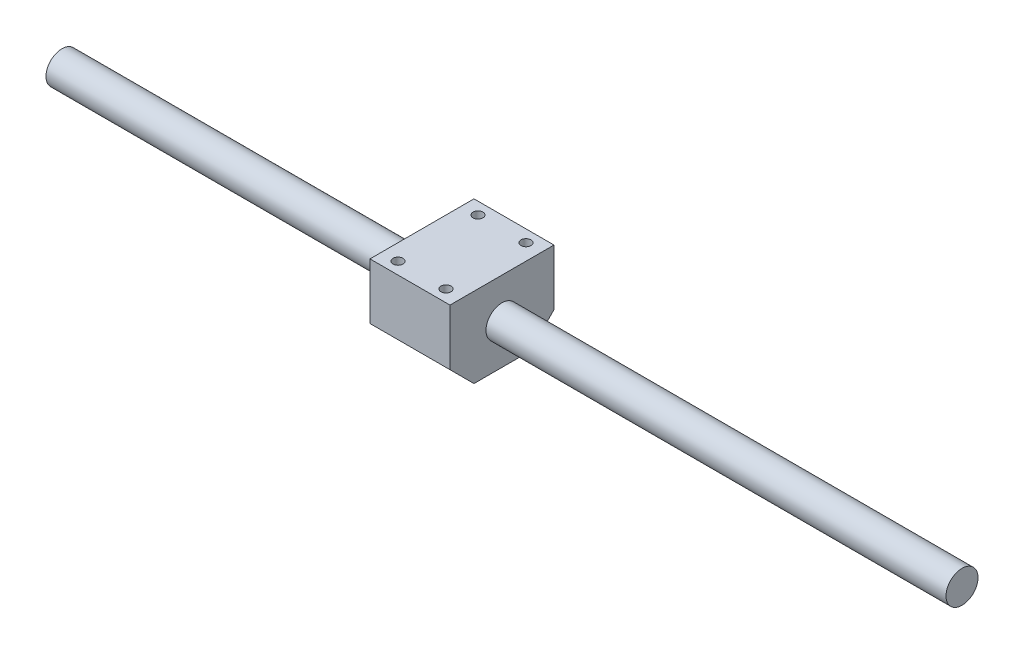
SolidWorks part; units mm, degrees
ref_plane "Front Plane" through (0, 0, 0) normal (0, 0, 1) x (1, 0, 0)
ref_plane "Top Plane" through (0, 0, 0) normal (0, 1, 0) x (1, 0, 0)
ref_plane "Right Plane" through (0, 0, 0) normal (1, 0, 0) x (0, 0, -1)
sketch "Sketch1" plane through (0, 0, 0) normal (1, 0, 0) x (0, 0, -1)
  circle A0 centre (0, 0) radius 8
  dimension "D1" = 16
extrude "Boss-Extrude1" add sketch "Sketch1" along normal blind 450
sketch "Sketch2" plane through (0, 0, 0) normal (0, 1, 0) x (1, 0, 0)
  line L0 (450, -8) -> (450, 8) construction
  line L1 (220, -26) -> (180, -26)
  line L2 (220, -26) -> (220, 26)
  line L3 (220, 26) -> (180, 26)
  line L4 (180, -26) -> (180, 26)
  line L5 (220, -26) -> (180, 26) construction
  line L6 (220, 26) -> (180, -26) construction
  point P0 (200, 0)
  dimension "D1" = 40
  dimension "D2" = 52
  dimension "D3" = 250
extrude "Boss-Extrude2" add sketch "Sketch2" along normal mid plane 40
chamfer "Chamfer1" distance 12 angle 45 2 edges at (200, -20, 26) (200, -20, -26)
sketch "Sketch3" plane through (0, 20, 0) normal (0, 1, 0) x (1, 0, 0)
  line L0 (180, 26) -> (220, 26) construction
  line L1 (212, -20) -> (188, -20) construction
  line L2 (212, -20) -> (212, 20) construction
  line L3 (212, 20) -> (188, 20) construction
  line L4 (188, -20) -> (188, 20) construction
  line L5 (212, -20) -> (188, 20) construction
  line L6 (212, 20) -> (188, -20) construction
  line L7 (220, -26) -> (220, 26) construction
  line L8 (220, 26) -> (180, 26) construction
  line L9 (220, 26) -> (220, -26) construction
  circle A0 centre (188, 20) radius 2.5
  circle A1 centre (212, 20) radius 2.5
  circle A2 centre (188, -20) radius 2.5
  circle A3 centre (212, -20) radius 2.5
  point P0 (200, 0)
  point P12 (200, 26)
  point P15 (220, 0)
  dimension "D3" = 5
  dimension "D1" = 40
  dimension "D2" = 24
extrude "Cut-Extrude1" cut sketch "Sketch3" against normal blind 10
